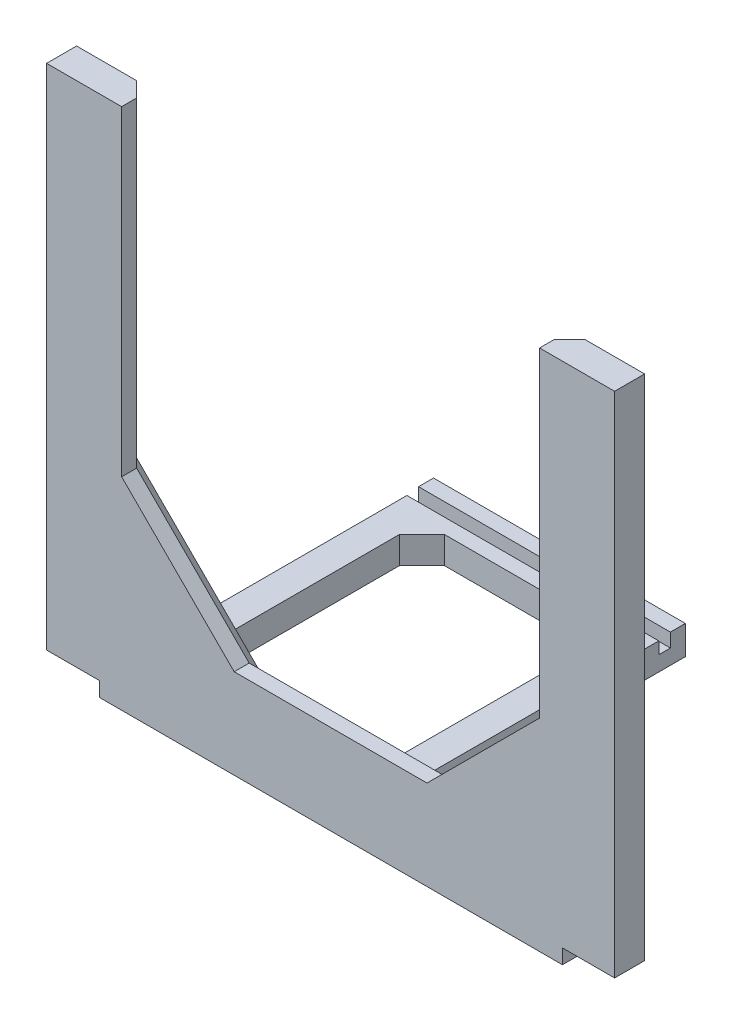
SolidWorks part; units mm, degrees
ref_plane "Płaszczyzna przednia" through (0, 0, 0) normal (0, 0, 1) x (1, 0, 0)
ref_plane "Płaszczyzna górna" through (0, 0, 0) normal (0, 1, 0) x (1, 0, 0)
ref_plane "Płaszczyzna prawa" through (0, 0, 0) normal (1, 0, 0) x (0, 0, -1)
sketch "Sketch6" plane through (0, 0, -103.809) normal (0, 0, -1) x (-1, 0, 0)
  line L1 (37.9172, -68.8813) -> (71.4815, -68.8813)
  line L2 (37.9172, -68.8813) -> (37.9172, -70.7201)
  line L3 (37.9172, -70.7201) -> (71.4815, -70.7201)
  line L4 (71.4815, -68.8813) -> (71.4815, -70.7201)
  dimension "D1" = 33.5642
  dimension "D2" = 1.8388
extrude "Boss-Extrude3" add sketch "Sketch6" along normal blind 2
sketch "Sketch7" plane through (0, -70.7201, 0) normal (0, -1, 0) x (1, 0, 0)
  line L0 (-71.4815, -105.809) -> (-71.4815, -103.809) construction
  line L1 (-37.9172, -105.809) -> (-71.4815, -105.809)
  line L2 (-37.9172, -105.809) -> (-37.9172, -100.259)
  line L3 (-37.9172, -100.259) -> (-71.4815, -100.259)
  line L4 (-71.4815, -105.809) -> (-71.4815, -100.259)
  dimension "D1" = 0
  dimension "D2" = 5.55
extrude "Boss-Extrude4" add sketch "Sketch7" along normal blind 2
sketch "Sketch8" plane through (-37.9172, 0, 0) normal (1, 0, 0) x (0, 0, -1)
  line L1 (100.259, -70.7201) -> (102.259, -70.7201)
  line L2 (100.259, -70.7201) -> (100.259, -69.1201)
  line L3 (100.259, -69.1201) -> (102.259, -69.1201)
  line L4 (102.259, -70.7201) -> (102.259, -69.1201)
  dimension "D1" = 2
  dimension "D2" = 1.6
extrude "Boss-Extrude5" add sketch "Sketch8" against normal up to surface (33.5642 mm away) up to face at (-71.4815, -70.7738, -103.2924)
sketch "Sketch9" plane through (0, 0, -100.259) normal (0, 0, 1) x (1, 0, 0)
  line L1 (-71.4815, -72.7201) -> (-67.4815, -72.7201)
  line L2 (-71.4815, -72.7201) -> (-71.4815, -69.1201)
  line L3 (-71.4815, -69.1201) -> (-67.4815, -69.1201)
  line L4 (-67.4815, -72.7201) -> (-67.4815, -69.1201)
  line L6 (-37.9172, -72.7201) -> (-41.9172, -72.7201)
  line L7 (-37.9172, -72.7201) -> (-37.9172, -69.1201)
  line L8 (-37.9172, -69.1201) -> (-41.9172, -69.1201)
  line L9 (-41.9172, -72.7201) -> (-41.9172, -69.1201)
  line L10 (-71.4815, -69.1201) -> (-37.9172, -69.1201) construction
  dimension "D1" = 4
  dimension "D2" = 4
  dimension "D3" = 0
  dimension "D4" = 0
extrude "Boss-Extrude6" add sketch "Sketch9" along normal up to surface (38.2037 mm away)
sketch "Sketch10" plane through (0, 0, -62.0553) normal (0, 0, 1) x (1, 0, 0)
  line L5 (-79.3, -70.7701) -> (-3.6, -70.7701)
  line L6 (-79.3, -70.7701) -> (-79.3, -60.7701)
  line L7 (-79.3, -60.7701) -> (-3.6, -60.7701)
  line L8 (-3.6, -70.7701) -> (-3.6, -60.7701)
  line L9 (-41.9172, -72.7201) -> (-67.4815, -72.7201) construction
  line L11 (-79.3, -60.7701) -> (-79.3, -3.05)
  line L12 (-79.3, -3.05) -> (-69.3, -3.05)
  line L15 (-79.3, -3.05) -> (-69.3, -3.05)
  line L16 (-79.3, -3.05) -> (-79.3, -70.7701)
  line L17 (-79.3, -70.7701) -> (-69.3, -70.7701)
  line L20 (-13.6, -3.05) -> (-3.6, -3.05)
  line L21 (-13.6, -3.05) -> (-13.6, -60.7701)
  line L22 (-13.6, -60.7701) -> (-3.6, -60.7701)
  line L23 (-3.6, -3.05) -> (-3.6, -60.7701)
  line L24 (-69.3, -3.05) -> (-69.3, -70.7701)
  line L31 (-74.2387, -70.8701) -> (-79.4, -70.8701) construction
  line L33 (-72.25, -70.7701) -> (-10.55, -70.7701)
  line L34 (-72.25, -70.7701) -> (-72.25, -72.7201)
  line L35 (-72.25, -72.7201) -> (-10.55, -72.7201)
  line L36 (-10.55, -70.7701) -> (-10.55, -72.7201)
  dimension "D2" = 0.1
  dimension "D3" = 61.7
  dimension "D4" = 0
  dimension "D5" = 0
  dimension "D6" = 75.7
  dimension "D7" = 57.7201
  dimension "D8" = 90
  dimension "D9" = 90
  dimension "D10" = 0
  dimension "D11" = 10
  dimension "D12" = 10
  dimension "D13" = 10
  dimension "D14" = 10
  dimension "D15" = 0
extrude "Boss-Extrude7" add sketch "Sketch10" against normal blind 4
chamfer "Chamfer2" distance 3 angle 45 8 edges at (-41.9172, -70.9201, -100.259) (-67.4815, -70.9201, -100.259) (-41.9172, -70.9201, -66.0553) (-39.9172, -69.1201, -66.0553) (-37.9172, -70.9201, -66.0553) (-67.4815, -70.9201, -66.0553) (-69.4815, -69.1201, -66.0553) (-71.4815, -70.9201, -66.0553)
chamfer "Chamfer5" distance 15 angle 45 2 edges at (-69.3, -60.7701, -64.0553) (-13.6, -60.7701, -64.0553)
sketch "Sketch11" plane through (0, 0, -66.0553) normal (0, 0, -1) x (-1, 0, 0)
  line L0 (79.3, -70.7701) -> (79.3, -3.05) construction
  line L2 (79.3, -3.05) -> (69.3, -3.05) construction
  line L3 (13.6, -3.05) -> (3.6, -3.05) construction
  line L4 (3.6, -70.7701) -> (3.6, -3.05) construction
  circle A3 centre (8.6, -6.55) radius 1.7
  circle A4 centre (74.3, -6.55) radius 1.7
  dimension "D8" = 3.4
  dimension "D9" = 3.4
  dimension "D10" = 3.5
  dimension "D11" = 5
  dimension "D12" = 3.5
  dimension "D13" = 5
extrude "Cut-Extrude1" cut sketch "Sketch11" against normal blind 3
chamfer "Chamfer7" distance 2 angle 45 5 edges at (-13.6, -24.41, -66.0553) (-21.1, -53.2701, -66.0553) (-41.45, -60.7701, -66.0553) (-61.8, -53.2701, -66.0553) (-69.3, -24.41, -66.0553)
